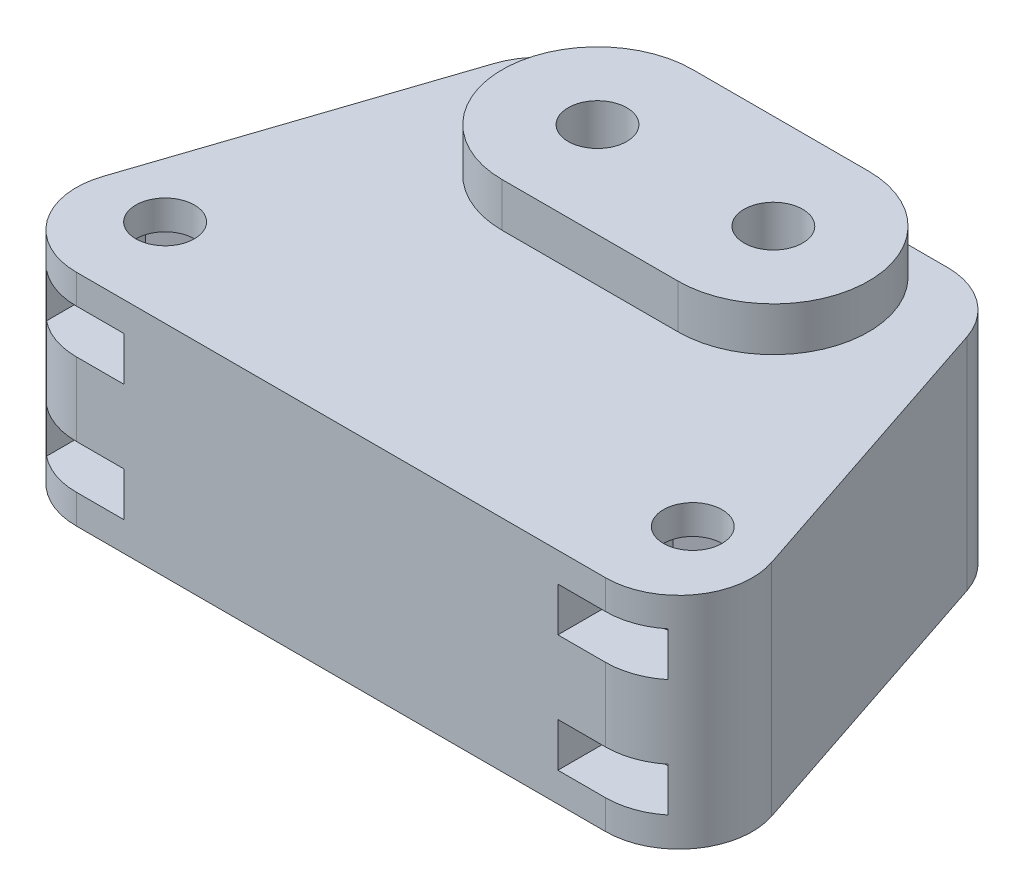
SolidWorks part; units mm, degrees
ref_plane "Front Plane" through (0, 0, 0) normal (0, 0, 1) x (1, 0, 0)
ref_plane "Top Plane" through (0, 0, 0) normal (0, 1, 0) x (1, 0, 0)
ref_plane "Right Plane" through (0, 0, 0) normal (1, 0, 0) x (0, 0, -1)
sketch "Sketch1" plane through (0, 0, 0) normal (0, 1, 0) x (1, 0, 0)
  line L0 (-18.0629, 0) -> (18.0629, 0)
  line L1 (22.8063, 6.5811) -> (16.1396, 26.5811)
  line L2 (11.3962, 30) -> (-11.3962, 30)
  line L3 (-16.1396, 26.5811) -> (-22.8063, 6.5811)
  line L4 (-25.9836, 23.5) -> (37.4439, 23.5) construction
  line L5 (42.967, 6) -> (-48.9088, 6) construction
  arc A0 (16.1396, 26.5811) -> (11.3962, 30) centre (11.3962, 25) ccw
  arc A1 (18.0629, 0) -> (22.8063, 6.5811) centre (18.0629, 5) ccw
  arc A2 (-18.0629, 0) -> (-22.8063, 6.5811) centre (-18.0629, 5) cw
  arc A3 (-11.3962, 30) -> (-16.1396, 26.5811) centre (-11.3962, 25) ccw
  circle A4 centre (-18, 6) radius 2
  circle A5 centre (18, 6) radius 2
  circle A6 centre (6, 23.5) radius 2
  circle A7 centre (-6, 23.5) radius 2
  point P7 (15, 30)
  point P10 (25, 0)
  point P13 (-25, 0)
  point P16 (-15, 30)
  point P27 (0, 30)
  point P28 (0, 0)
  dimension "D6" = 5
  dimension "D7" = 4
  dimension "D8" = 6
  dimension "D12" = 17.5
  dimension "D1" = 50
  dimension "D2" = 30
  dimension "D3" = 15
  dimension "D4" = 25
  dimension "D5" = 30
  dimension "D9" = 12
  dimension "D10" = 36
  dimension "D11" = 18
  dimension "D13" = 6
extrude "Boss-Extrude1" add sketch "Sketch1" along normal blind 15
sketch "Sketch2" plane through (0, 15, 0) normal (0, 1, 0) x (1, 0, 0)
  line L0 (-6, 23.5) -> (6, 23.5) construction
  line L1 (-6, 23.5) -> (6, 23.5) construction
  line L2 (-6, 30) -> (6, 30)
  line L3 (-6, 17) -> (6, 17)
  line L4 (11.3962, 30) -> (-11.3962, 30) construction
  arc A0 (-6, 30) -> (-6, 17) centre (-6, 23.5) ccw
  arc A1 (6, 17) -> (6, 30) centre (6, 23.5) ccw
  circle A2 centre (-6, 23.5) radius 2
  circle A3 centre (6, 23.5) radius 2
  point P4 (0, 23.5)
extrude "Boss-Extrude2" add sketch "Sketch2" along normal blind 3
sketch "Sketch5" plane through (0, 0, -30) normal (0, 0, -1) x (-1, 0, 0)
  line L1 (9.2, 11) -> (2.8, 11)
  line L2 (9.2, 11) -> (9.2, 14)
  line L3 (9.2, 14) -> (2.8, 14)
  line L4 (2.8, 11) -> (2.8, 14)
  line L5 (-2.8, 11) -> (-9.2, 11)
  line L6 (-2.8, 11) -> (-2.8, 14)
  line L7 (-2.8, 14) -> (-9.2, 14)
  line L8 (-9.2, 11) -> (-9.2, 14)
  line L9 (-11.3962, 0) -> (11.3962, 0) construction
  line L10 (6, 15) -> (11.3962, 15) construction
  line L11 (-9.2, 5) -> (-2.8, 5)
  line L12 (-9.2, 5) -> (-9.2, 2)
  line L13 (-9.2, 2) -> (-2.8, 2)
  line L14 (-2.8, 5) -> (-2.8, 2)
  line L15 (2.8, 5) -> (9.2, 5)
  line L16 (2.8, 5) -> (2.8, 2)
  line L17 (2.8, 2) -> (9.2, 2)
  line L18 (9.2, 5) -> (9.2, 2)
  point P8 (-2.8, 12.5)
  point P11 (0, 0)
  dimension "D1" = 6.4
  dimension "D2" = 6.4
  dimension "D3" = 3
  dimension "D4" = 3
  dimension "D5" = 2.8
  dimension "D6" = 2.8
  dimension "D7" = 4
  dimension "D8" = 3
  dimension "D9" = 3
  dimension "D10" = 6.4
  dimension "D11" = 6.4
  dimension "D12" = 2
extrude "Cut-Extrude1" cut sketch "Sketch5" against normal blind 6.4
sketch "Sketch6" plane through (0, 11, 0) normal (0, 1, 0) x (1, 0, 0)
  line L0 (-2.8, 23.6) -> (-2.8, 30) construction
  line L1 (9.2, 25.3475) -> (6, 27.195)
  line L2 (6, 27.195) -> (2.8, 25.3475)
  line L3 (2.8, 25.3475) -> (2.8, 21.6525)
  line L4 (2.8, 21.6525) -> (6, 19.805)
  line L5 (6, 19.805) -> (9.2, 21.6525)
  line L6 (9.2, 21.6525) -> (9.2, 25.3475)
  line L7 (-2.8, 25.3475) -> (-6, 27.195)
  line L8 (-6, 27.195) -> (-9.2, 25.3475)
  line L9 (-9.2, 25.3475) -> (-9.2, 21.6525)
  line L10 (-9.2, 21.6525) -> (-6, 19.805)
  line L11 (-6, 19.805) -> (-2.8, 21.6525)
  line L12 (-2.8, 21.6525) -> (-2.8, 25.3475)
  line L13 (9.2, 23.6) -> (9.2, 30) construction
  circle A0 centre (6, 23.5) radius 3.2 construction
  circle A1 centre (-6, 23.5) radius 3.2 construction
extrude "Cut-Extrude2" cut sketch "Sketch6" along normal up to surface (3 mm away) up to face at (6, 14, -26.05)
sketch "Sketch7" plane through (0, 2, 0) normal (0, 1, 0) x (1, 0, 0)
  line L6 (9.2, 25.3475) -> (6, 27.195)
  line L7 (6, 27.195) -> (2.8, 25.3475)
  line L8 (2.8, 25.3475) -> (2.8, 21.6525)
  line L9 (2.8, 21.6525) -> (6, 19.805)
  line L10 (6, 19.805) -> (9.2, 21.6525)
  line L11 (9.2, 21.6525) -> (9.2, 25.3475)
  line L12 (9.2, 25.3475) -> (6, 27.195)
  line L13 (6, 27.195) -> (2.8, 25.3475)
  line L14 (2.8, 25.3475) -> (2.8, 21.6525)
  line L15 (2.8, 21.6525) -> (6, 19.805)
  line L16 (6, 19.805) -> (9.2, 21.6525)
  line L17 (9.2, 21.6525) -> (9.2, 25.3475)
  line L18 (-6, 19.805) -> (-2.8, 21.6525)
  line L19 (-9.2, 21.6525) -> (-6, 19.805)
  line L20 (-9.2, 25.3475) -> (-9.2, 21.6525)
  line L21 (-6, 27.195) -> (-9.2, 25.3475)
  line L22 (-2.8, 25.3475) -> (-6, 27.195)
  line L23 (-2.8, 21.6525) -> (-2.8, 25.3475)
  line L24 (-6, 19.805) -> (-2.8, 21.6525)
  line L25 (-9.2, 21.6525) -> (-6, 19.805)
  line L26 (-9.2, 25.3475) -> (-9.2, 21.6525)
  line L27 (-6, 27.195) -> (-9.2, 25.3475)
  line L28 (-2.8, 25.3475) -> (-6, 27.195)
  line L29 (-2.8, 21.6525) -> (-2.8, 25.3475)
  dimension "D1" = 0
  dimension "D2" = 0
extrude "Cut-Extrude3" cut sketch "Sketch7" along normal up to surface (3 mm away) up to face at (6, 5, -26.05)
sketch "Sketch8" plane through (0, 0, 0) normal (0, 0, 1) x (1, 0, 0)
  line L0 (-18.0629, 0) -> (18.0629, 0) construction
  line L1 (21.2, 13) -> (14.8, 13)
  line L2 (21.2, 13) -> (21.2, 10)
  line L3 (21.2, 10) -> (14.8, 10)
  line L4 (14.8, 13) -> (14.8, 10)
  line L5 (-14.8, 13) -> (-21.2, 13)
  line L6 (-14.8, 13) -> (-14.8, 10)
  line L7 (-14.8, 10) -> (-21.2, 10)
  line L8 (-21.2, 13) -> (-21.2, 10)
  line L9 (-14.8, 5) -> (-21.2, 5)
  line L10 (-14.8, 5) -> (-14.8, 2)
  line L11 (-14.8, 2) -> (-21.2, 2)
  line L12 (-21.2, 5) -> (-21.2, 2)
  line L13 (21.2, 5) -> (14.8, 5)
  line L14 (21.2, 5) -> (21.2, 2)
  line L15 (21.2, 2) -> (14.8, 2)
  line L16 (14.8, 5) -> (14.8, 2)
  line L17 (-18.0629, 15) -> (18.0629, 15) construction
  point P16 (18, 10)
  point P18 (-18, 2)
  dimension "D1" = 3
  dimension "D2" = 6.4
  dimension "D3" = 18
  dimension "D4" = 18
  dimension "D5" = 2
  dimension "D6" = 2
extrude "Cut-Extrude4" cut sketch "Sketch8" against normal blind 6
sketch "Sketch9" plane through (0, 10, 0) normal (0, 1, 0) x (1, 0, 0)
  line L0 (-14.8, 6) -> (-14.8, 0) construction
  line L1 (21.2, 4.1525) -> (21.2, 7.8475)
  line L2 (21.2, 7.8475) -> (18, 9.695)
  line L3 (18, 9.695) -> (14.8, 7.8475)
  line L4 (14.8, 7.8475) -> (14.8, 4.1525)
  line L5 (14.8, 4.1525) -> (18, 2.305)
  line L6 (18, 2.305) -> (21.2, 4.1525)
  line L7 (-14.8, 4.1525) -> (-14.8, 7.8475)
  line L8 (-14.8, 7.8475) -> (-18, 9.695)
  line L9 (-18, 9.695) -> (-21.2, 7.8475)
  line L10 (-21.2, 7.8475) -> (-21.2, 4.1525)
  line L11 (-21.2, 4.1525) -> (-18, 2.305)
  line L12 (-18, 2.305) -> (-14.8, 4.1525)
  line L13 (21.2, 6) -> (21.2, 1.1066) construction
  circle A0 centre (18, 6) radius 3.2 construction
  circle A1 centre (-18, 6) radius 3.2 construction
extrude "Cut-Extrude5" cut sketch "Sketch9" along normal up to surface (3 mm away) up to face at (18.0225, 13, -3.2626)
sketch "Sketch10" plane through (0, 2, 0) normal (0, 1, 0) x (1, 0, 0)
  line L6 (21.2, 4.1525) -> (21.2, 7.8475)
  line L7 (21.2, 7.8475) -> (18, 9.695)
  line L8 (18, 9.695) -> (14.8, 7.8475)
  line L9 (14.8, 7.8475) -> (14.8, 4.1525)
  line L10 (14.8, 4.1525) -> (18, 2.305)
  line L11 (18, 2.305) -> (21.2, 4.1525)
  line L12 (21.2, 4.1525) -> (21.2, 7.8475)
  line L13 (21.2, 7.8475) -> (18, 9.695)
  line L14 (18, 9.695) -> (14.8, 7.8475)
  line L15 (14.8, 7.8475) -> (14.8, 4.1525)
  line L16 (14.8, 4.1525) -> (18, 2.305)
  line L17 (18, 2.305) -> (21.2, 4.1525)
  line L18 (-21.2, 4.1525) -> (-18, 2.305)
  line L19 (-21.2, 7.8475) -> (-21.2, 4.1525)
  line L20 (-18, 9.695) -> (-21.2, 7.8475)
  line L21 (-14.8, 7.8475) -> (-18, 9.695)
  line L22 (-14.8, 4.1525) -> (-14.8, 7.8475)
  line L23 (-18, 2.305) -> (-14.8, 4.1525)
  line L24 (-21.2, 4.1525) -> (-18, 2.305)
  line L25 (-21.2, 7.8475) -> (-21.2, 4.1525)
  line L26 (-18, 9.695) -> (-21.2, 7.8475)
  line L27 (-14.8, 7.8475) -> (-18, 9.695)
  line L28 (-14.8, 4.1525) -> (-14.8, 7.8475)
  line L29 (-18, 2.305) -> (-14.8, 4.1525)
  dimension "D1" = 0
  dimension "D2" = 0
extrude "Cut-Extrude6" cut sketch "Sketch10" along normal up to surface (3 mm away) up to face at (18.0225, 5, -3.2626)
